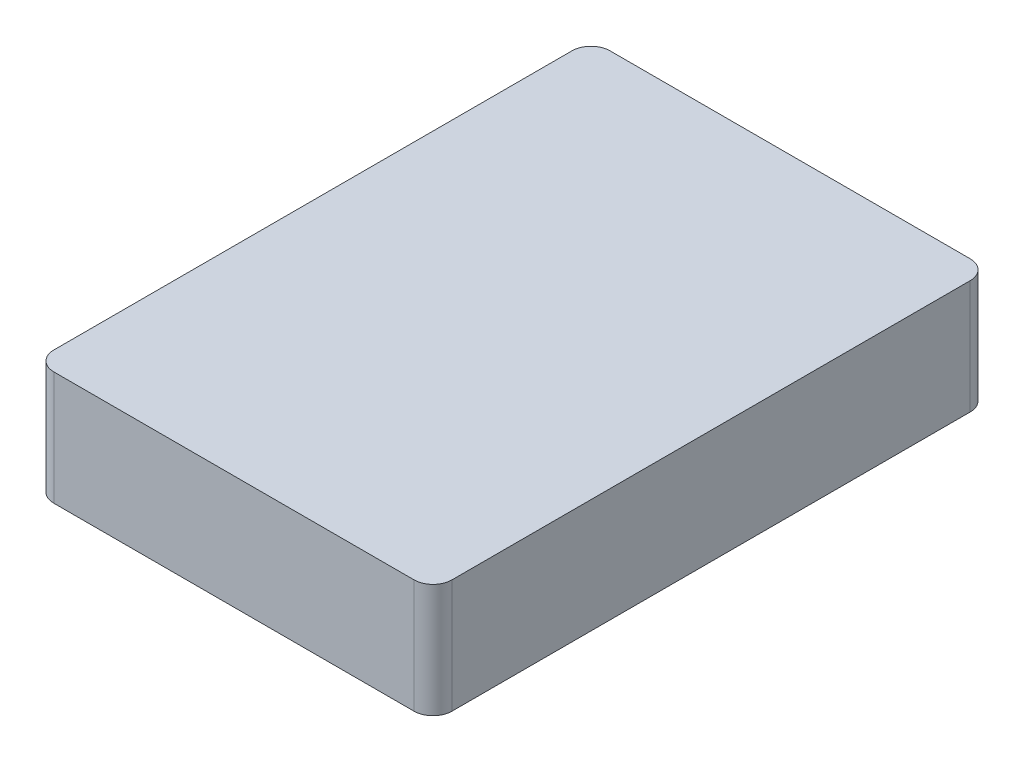
SolidWorks part; units mm, degrees
ref_plane "Front Plane" through (0, 0, 0) normal (0, 0, 1) x (1, 0, 0)
ref_plane "Top Plane" through (0, 0, 0) normal (0, 1, 0) x (1, 0, 0)
ref_plane "Right Plane" through (0, 0, 0) normal (1, 0, 0) x (0, 0, -1)
sketch "Sketch1" plane through (0, 0, 0) normal (0, 1, 0) x (1, 0, 0)
  line L1 (28.5, -44) -> (-28.5, -44)
  line L2 (31.5, -41) -> (31.5, 41)
  line L3 (28.5, 44) -> (-28.5, 44)
  line L4 (-31.5, -41) -> (-31.5, 41)
  line L5 (31.5, -44) -> (-31.5, 44) construction
  line L6 (31.5, 44) -> (-31.5, -44) construction
  arc A0 (-28.5, -44) -> (-31.5, -41) centre (-28.5, -41) cw
  arc A1 (28.5, -44) -> (31.5, -41) centre (28.5, -41) ccw
  arc A2 (31.5, 41) -> (28.5, 44) centre (28.5, 41) ccw
  arc A3 (-28.5, 44) -> (-31.5, 41) centre (-28.5, 41) ccw
  point P0 (0, 0)
  dimension "D3" = 3
  dimension "D1" = 88
  dimension "D2" = 63
extrude "Boss-Extrude1" add sketch "Sketch1" along normal blind 18
